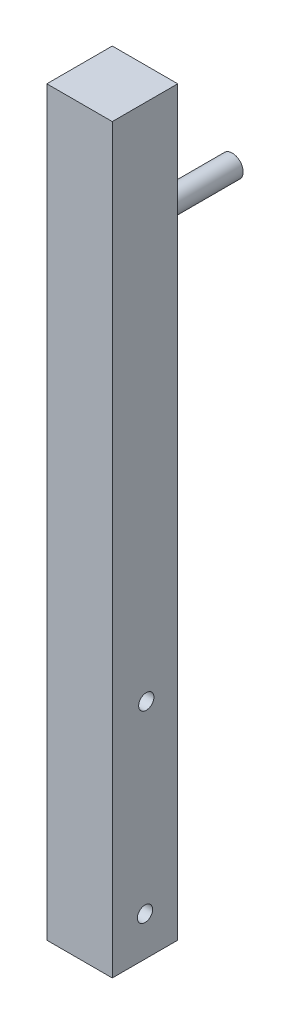
SolidWorks part; units mm, degrees
ref_plane "Front Plane" through (0, 0, 0) normal (0, 0, 1) x (1, 0, 0)
ref_plane "Top Plane" through (0, 0, 0) normal (0, 1, 0) x (1, 0, 0)
ref_plane "Right Plane" through (0, 0, 0) normal (1, 0, 0) x (0, 0, -1)
sketch "Sketch1" plane through (0, 0, 0) normal (0, 1, 0) x (1, 0, 0)
  line L1 (-7.5, 7.5) -> (7.5, 7.5)
  line L2 (-7.5, 7.5) -> (-7.5, -7.5)
  line L3 (-7.5, -7.5) -> (7.5, -7.5)
  line L4 (7.5, 7.5) -> (7.5, -7.5)
  point P4 (0, 7.5)
  point P6 (-7.5, 0)
  dimension "D1" = 15
  dimension "D2" = 15
extrude "Boss-Extrude1" add sketch "Sketch1" along normal blind 170
sketch "Sketch2" plane through (7.5, 0, 0) normal (1, 0, 0) x (0, 0, -1)
  line L0 (-7.5, 0) -> (7.5, 0) construction
  line L1 (7.5, 170) -> (7.5, 0) construction
  circle A0 centre (0, 9) radius 1.75
  circle A1 centre (0.2953, 51) radius 1.75
  dimension "D1" = 9
  dimension "D2" = 42
  dimension "D3" = 7.5
extrude "Cut-Extrude1" cut sketch "Sketch2" against normal through all
sketch "Sketch3" plane through (-7.5, 0, 0) normal (-1, 0, 0) x (0, 0, 1)
  line L0 (-7.5, 170) -> (7.5, 170) construction
  circle A0 centre (0, 161) radius 4.05
  circle A1 centre (0, 119) radius 4.05
  dimension "D1" = 9
  dimension "D2" = 42
extrude "Cut-Extrude2" cut sketch "Sketch3" against normal blind 10
sketch "Sketch5" plane through (0, 0, -7.5) normal (0, 0, -1) x (-1, 0, 0)
  line L0 (-7.5, 170) -> (-7.5, 0) construction
  line L1 (-7.5, 170) -> (7.5, 170) construction
  circle A0 centre (0, 140) radius 2.5
  dimension "D1" = 7.5
  dimension "D2" = 30
extrude "Boss-Extrude3" add sketch "Sketch5" along normal blind 20
